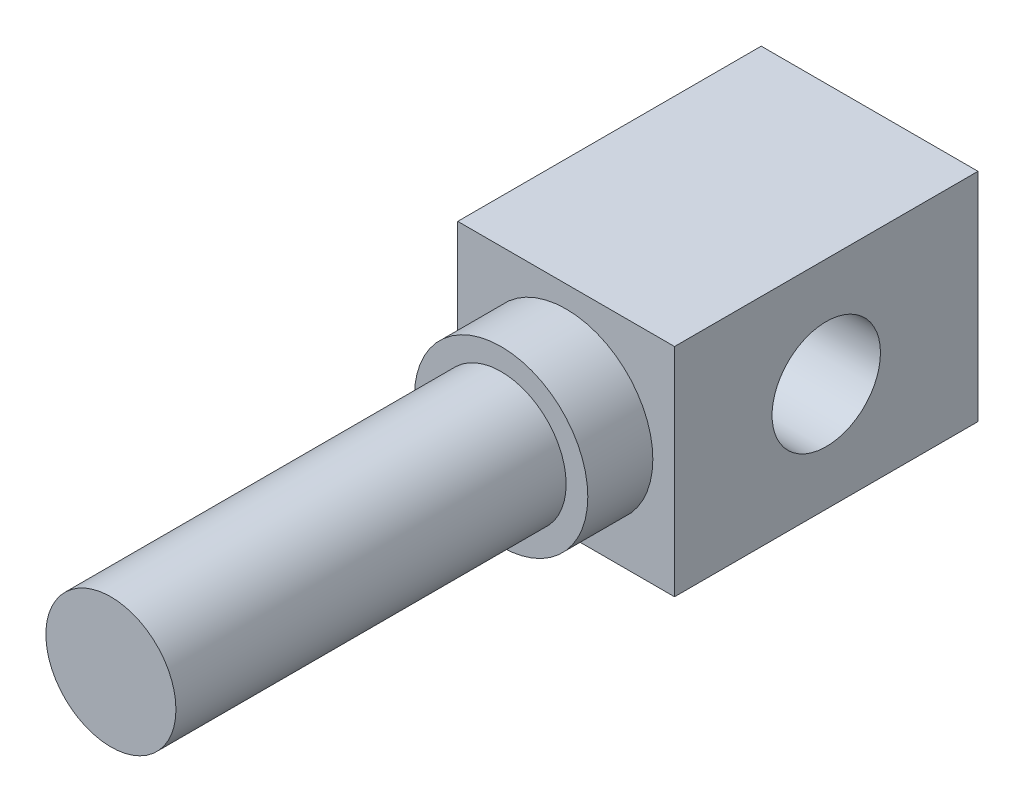
SolidWorks part; units mm, degrees
material "3003-H16"
ref_plane "前视基准面" through (0, 0, 0) normal (0, 0, 1) x (1, 0, 0)
ref_plane "上视基准面" through (0, 0, 0) normal (0, 1, 0) x (1, 0, 0)
ref_plane "右视基准面" through (0, 0, 0) normal (1, 0, 0) x (0, 0, -1)
sketch "草图1" plane through (0, 0, 0) normal (0, 0, 1) x (1, 0, 0)
  line L1 (0, 0) -> (5, 0)
  line L2 (0, 0) -> (0, 5)
  line L3 (0, 5) -> (5, 5)
  line L4 (5, 0) -> (5, 5)
  dimension "D1" = 5
  dimension "D2" = 5
extrude "凸台-拉伸1" add sketch "草图1" along normal blind 7
sketch "草图2" plane through (0, 0, 7) normal (0, 0, 1) x (1, 0, 0)
  line L0 (5, 0) -> (5, 5) construction
  circle A0 centre (2.5, 2.5) radius 2
  dimension "D1" = 2.5
  dimension "D2" = 2.5
extrude "凸台-拉伸2" add sketch "草图2" along normal blind 1.5
sketch "草图3" plane through (0, 0, 8.5) normal (0, 0, 1) x (1, 0, 0)
  circle A0 centre (2.5, 2.5) radius 1.5
  dimension "D1" = 3
extrude "凸台-拉伸3" add sketch "草图3" along normal blind 9
hole_wizard "M3 螺纹孔2" positions "3D草图2" profile "草图6" tap size "M3" standard "ISO"
sketch3d "3D草图2"
  line L0 (5, 0, 7) -> (5, 0, 0) construction
  line L1 (5, 0, 0) -> (5, 5, 0) construction
  point P0 (5, 2.5, 3.5)
  dimension "D1" = 2.5
  dimension "D2" = 3.5
sketch "草图6" plane through (5, 2.5, 3.5) normal (0, 1, 0) x (0, 0, -1)
  line L0 (0, 0) -> (0, 8.2511)
  line L1 (0, 8.2511) -> (1.25, 7.5)
  line L2 (1.25, 7.5) -> (1.25, 0)
  line L5 (1.25, 0) -> (0, 0)
  line L10 (0, 8.2511) -> (-1.25, 7.5) construction
  line L11 (0, -6.35) -> (0, 107.95) construction
  dimension "螺纹孔钻头直径" = 2.5
  dimension "螺纹孔钻头深度" = 7.5
  dimension "导头角度" = 118
cosmetic thread "孔螺蚊线2" parameters "D1"=5, "D2"=3
